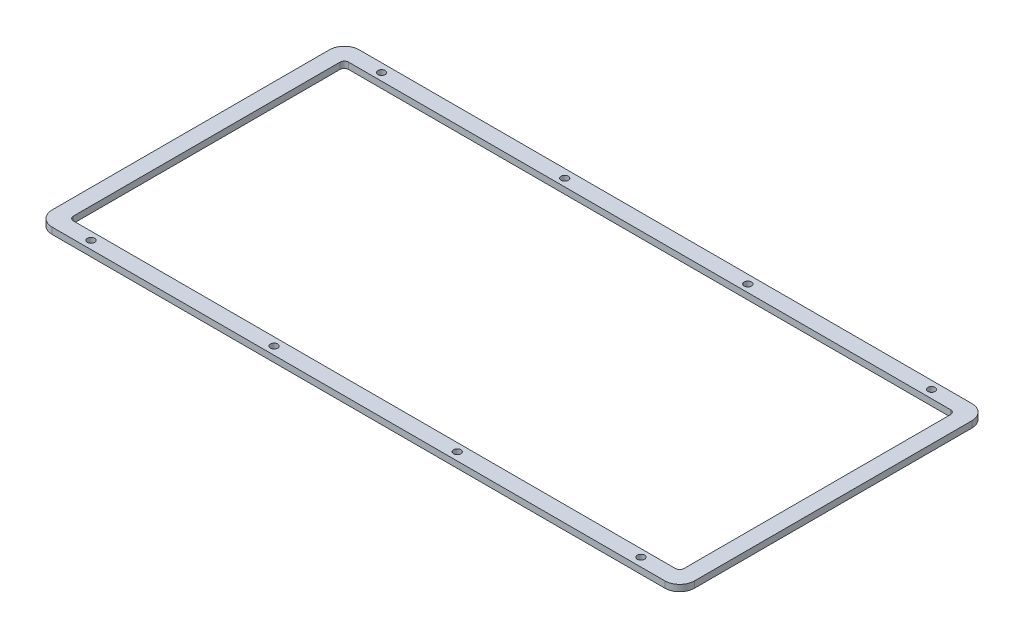
SolidWorks part; units mm, degrees
ref_plane "Front Plane" through (0, 0, 0) normal (0, 0, 1) x (1, 0, 0)
ref_plane "Top Plane" through (0, 0, 0) normal (0, 1, 0) x (1, 0, 0)
ref_plane "Right Plane" through (0, 0, 0) normal (1, 0, 0) x (0, 0, -1)
sketch "Sketch1" plane through (0, 0, 0) normal (0, 1, 0) x (1, 0, 0)
  line L1 (0, 0) -> (350, 0)
  line L2 (0, 0) -> (0, 200)
  line L3 (0, 200) -> (350, 200)
  line L4 (350, 0) -> (350, 200)
extrude "Boss-Extrude1" add sketch "Sketch1" along normal blind 3
sketch "Sketch2" plane through (0, 3, 0) normal (0, 1, 0) x (1, 0, 0)
  line L0 (33.2846, 167.3458) -> (315.9839, 167.3458)
  line L1 (317.9839, 165.3458) -> (317.9839, 40.1464)
  line L2 (315.9839, 38.1464) -> (33.2846, 38.1464)
  line L3 (31.2846, 40.1464) -> (31.2846, 165.3458)
  line L4 (23.7846, 37.6464) -> (23.7846, 167.8458)
  line L5 (318.4839, 30.6464) -> (30.7846, 30.6464)
  line L6 (325.4839, 167.8458) -> (325.4839, 37.6464)
  line L7 (30.7846, 174.8458) -> (318.4839, 174.8458)
  arc A0 (33.2846, 167.3458) -> (31.2846, 165.3458) centre (33.2846, 165.3458) ccw
  arc A1 (317.9839, 165.3458) -> (315.9839, 167.3458) centre (315.9839, 165.3458) ccw
  arc A2 (315.9839, 38.1464) -> (317.9839, 40.1464) centre (315.9839, 40.1464) ccw
  arc A3 (31.2846, 40.1464) -> (33.2846, 38.1464) centre (33.2846, 40.1464) ccw
  circle A4 centre (303.2846, 34.6464) radius 1.7
  circle A5 centre (217.2846, 34.3964) radius 1.7
  circle A6 centre (45.2846, 34.3964) radius 1.7
  circle A7 centre (131.2846, 34.3964) radius 1.7
  circle A8 centre (303.2846, 171.0958) radius 1.7
  circle A9 centre (217.2846, 170.8458) radius 1.7
  circle A10 centre (45.2846, 170.8458) radius 1.7
  circle A11 centre (131.2846, 170.8458) radius 1.7
  arc A12 (30.7846, 174.8458) -> (23.7846, 167.8458) centre (30.7846, 167.8458) ccw
  arc A13 (23.7846, 37.6464) -> (30.7846, 30.6464) centre (30.7846, 37.6464) ccw
  arc A14 (318.4839, 30.6464) -> (325.4839, 37.6464) centre (318.4839, 37.6464) ccw
  arc A15 (325.4839, 167.8458) -> (318.4839, 174.8458) centre (318.4839, 167.8458) ccw
extrude "Cut-Extrude1" cut sketch "Sketch2" against normal blind 10 flip side to cut
